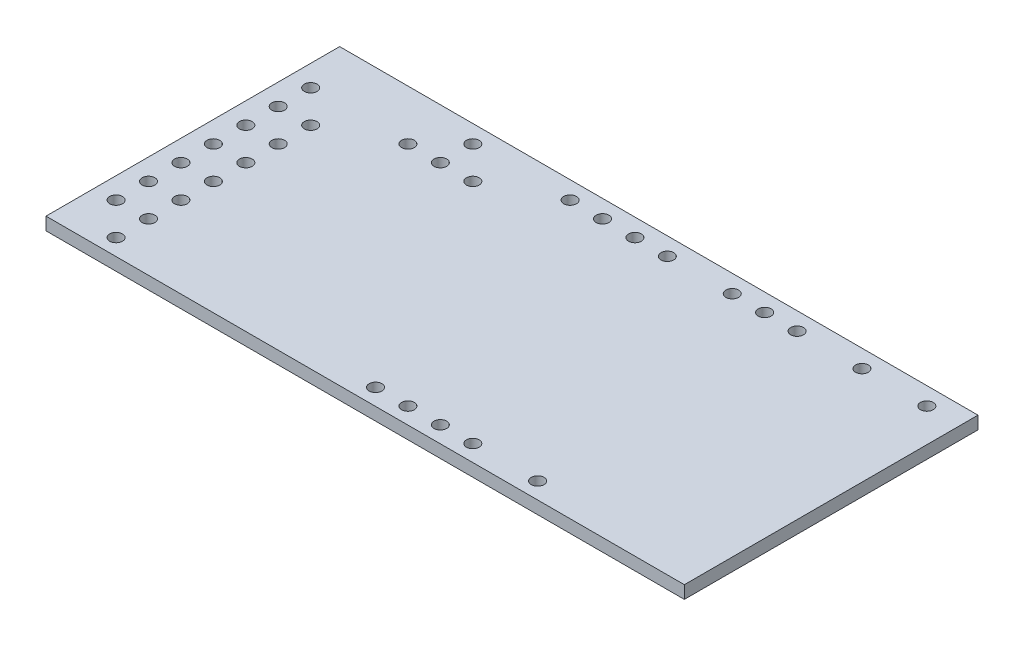
SolidWorks part; units mm, degrees
ref_plane "Front Plane" through (0, 0, 0) normal (0, 0, 1) x (1, 0, 0)
ref_plane "Top Plane" through (0, 0, 0) normal (0, 1, 0) x (1, 0, 0)
ref_plane "Right Plane" through (0, 0, 0) normal (1, 0, 0) x (0, 0, -1)
sketch "Sketch1" plane through (0, 0, 0) normal (0, 1, 0) x (1, 0, 0)
  line L1 (0, 0) -> (50, 0)
  line L2 (0, 0) -> (0, 23)
  line L3 (0, 23) -> (50, 23)
  line L4 (50, 0) -> (50, 23)
  dimension "D1" = 23
  dimension "D2" = 50
extrude "Boss-Extrude1" add sketch "Sketch1" along normal blind 1
sketch "Sketch2" plane through (0, 1, 0) normal (0, 1, 0) x (1, 0, 0)
  line L0 (0, 23) -> (0, 0) construction
  line L1 (0, 0) -> (50, 0) construction
  circle A0 centre (1.66, 3.83) radius 0.5
  circle A1 centre (4.2, 3.83) radius 0.5
  circle A2 centre (1.66, 6.37) radius 0.5
  circle A3 centre (1.66, 8.91) radius 0.5
  circle A4 centre (1.66, 11.45) radius 0.5
  circle A5 centre (1.66, 13.99) radius 0.5
  circle A6 centre (1.66, 16.53) radius 0.5
  circle A7 centre (1.66, 19.07) radius 0.5
  circle A8 centre (4.2, 6.37) radius 0.5
  circle A9 centre (4.2, 8.91) radius 0.5
  circle A10 centre (4.2, 11.45) radius 0.5
  circle A11 centre (4.2, 13.99) radius 0.5
  circle A12 centre (4.2, 16.53) radius 0.5
  circle A13 centre (4.2, 1.29) radius 0.5
  circle A14 centre (4.2, 19.07) radius 0.5 [skipped]
  circle A15 centre (6.74, 19.07) radius 0.5 [skipped]
  circle A16 centre (9.28, 19.07) radius 0.5
  circle A17 centre (11.82, 19.07) radius 0.5
  circle A18 centre (14.36, 19.07) radius 0.5
  circle A19 centre (11.82, 21.61) radius 0.5
  circle A20 centre (14.36, 21.61) radius 0.5 [skipped]
  circle A21 centre (16.9, 21.61) radius 0.5 [skipped]
  circle A22 centre (19.44, 21.61) radius 0.5
  circle A23 centre (21.98, 21.61) radius 0.5
  circle A24 centre (24.52, 21.61) radius 0.5
  circle A25 centre (27.06, 21.61) radius 0.5
  circle A26 centre (29.6, 21.61) radius 0.5 [skipped]
  circle A27 centre (32.14, 21.61) radius 0.5
  circle A28 centre (34.68, 21.61) radius 0.5
  circle A29 centre (37.22, 21.61) radius 0.5
  circle A30 centre (39.76, 21.61) radius 0.5 [skipped]
  circle A31 centre (42.3, 21.61) radius 0.5
  circle A32 centre (44.84, 21.61) radius 0.5 [skipped]
  circle A33 centre (47.38, 21.61) radius 0.5
  circle A34 centre (6.74, 1.29) radius 0.5 [skipped]
  circle A35 centre (9.28, 1.29) radius 0.5 [skipped]
  circle A36 centre (11.82, 1.29) radius 0.5 [skipped]
  circle A37 centre (14.36, 1.29) radius 0.5 [skipped]
  circle A38 centre (16.9, 1.29) radius 0.5 [skipped]
  circle A39 centre (19.44, 1.29) radius 0.5 [skipped]
  circle A40 centre (21.98, 1.29) radius 0.5 [skipped]
  circle A41 centre (24.52, 1.29) radius 0.5
  circle A42 centre (27.06, 1.29) radius 0.5
  circle A43 centre (29.6, 1.29) radius 0.5
  circle A44 centre (32.14, 1.29) radius 0.5
  circle A45 centre (34.68, 1.29) radius 0.5 [skipped]
  circle A46 centre (37.22, 1.29) radius 0.5
  dimension "D1" = 1
  dimension "D5" = 7
  dimension "D2" = 1.66
  dimension "D3" = 3.83
  dimension "D4" = 2.54
  dimension "D6" = 6
  dimension "D7" = 2
  dimension "D8" = 6
  dimension "D9" = 2
  dimension "D10" = 15
  dimension "D11" = 14
extrude "Cut-Extrude1" cut sketch "Sketch2" against normal through all
